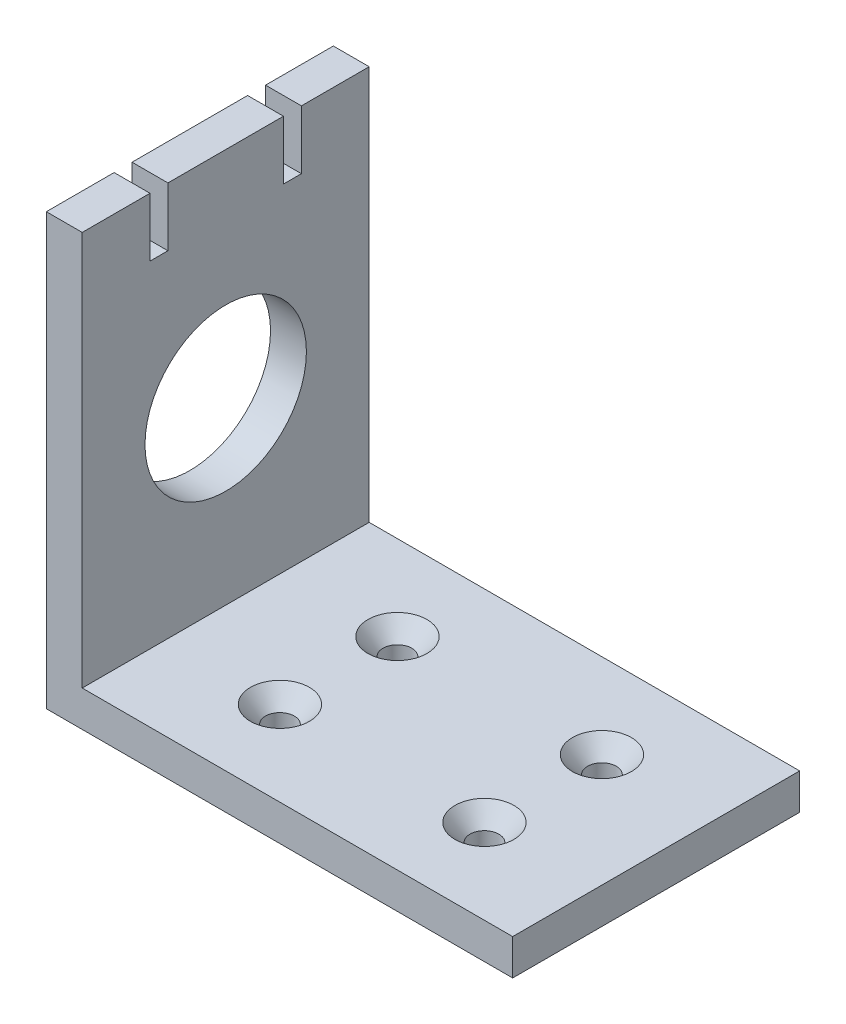
SolidWorks part; units mm, degrees
ref_plane "Front Plane" through (0, 0, 0) normal (0, 0, 1) x (1, 0, 0)
ref_plane "Top Plane" through (0, 0, 0) normal (0, 1, 0) x (1, 0, 0)
ref_plane "Right Plane" through (0, 0, 0) normal (1, 0, 0) x (0, 0, -1)
sketch "Sketch1" plane through (0, 0, 0) normal (1, 0, 0) x (0, 0, -1)
  line L1 (0, 0) -> (50.8, 0)
  line L2 (0, 0) -> (0, 76.2)
  line L3 (0, 76.2) -> (50.8, 76.2)
  line L4 (50.8, 0) -> (50.8, 76.2)
  dimension "D1" = 76.2
  dimension "D2" = 50.8
extrude "Boss-Extrude1" add sketch "Sketch1" along normal blind 6.35
sketch "Sketch2" plane through (6.35, 0, 0) normal (1, 0, 0) x (0, 0, -1)
  line L0 (50.8, 0) -> (50.8, 76.2) construction
  line L1 (0, 0) -> (50.8, 0)
  line L2 (0, 0) -> (0, 6.35)
  line L3 (0, 6.35) -> (50.8, 6.35)
  line L4 (50.8, 0) -> (50.8, 6.35)
  dimension "D1" = 6.35
extrude "Boss-Extrude2" add sketch "Sketch2" along normal blind 76.2
sketch "Sketch3" plane through (6.35, 0, 0) normal (1, 0, 0) x (0, 0, -1)
  line L0 (0, 0) -> (50.8, 0) construction
  line L1 (0, 76.2) -> (0, 6.35) construction
  circle A0 centre (25.4, 38.1) radius 14.2875
  dimension "D1" = 28.575
  dimension "D2" = 38.1
  dimension "D3" = 25.4
extrude "Cut-Extrude1" cut sketch "Sketch3" against normal through all
hole_wizard "CSK for #10 Flat Head Socket Cap Screw1" positions "Sketch10" profile "Sketch11" countersink size "#10" standard "ANSI Inch" end condition through all
sketch "Sketch10" plane through (0, 6.35, 0) normal (0, 1, 0) x (1, 0, 0)
  line L3 (82.55, 50.8) -> (6.35, 50.8) construction
  line L4 (82.55, 0) -> (6.35, 0) construction
  line L5 (6.35, 50.8) -> (6.35, 0) construction
  line L6 (6.35, 50.8) -> (6.35, 0) construction
  line L7 (82.55, 50.8) -> (82.55, 0) construction
  point P0 (26.35, 35.8)
  point P2 (62.55, 35.8)
  point P4 (62.55, 15)
  point P6 (26.35, 15)
  dimension "D1" = 15
  dimension "D2" = 15
  dimension "D3" = 15
  dimension "D4" = 15
  dimension "D5" = 20
  dimension "D6" = 20
  dimension "D7" = 20
  dimension "D8" = 20
sketch "Sketch11" plane through (26.35, 6.35, -35.8) normal (1, 0, 0) x (0, 0, 1)
  line L0 (0, 0) -> (0, 6.35)
  line L1 (0, 6.35) -> (2.5527, 6.35)
  line L2 (2.5527, 6.35) -> (2.5527, 3.068)
  line L3 (2.5527, 3.068) -> (5.2197, 0)
  line L5 (5.2197, 0) -> (0, 0)
  line L6 (-2.5527, 3.068) -> (-5.2197, 0) construction
  line L11 (0, -6.35) -> (0, 107.95) construction
  dimension "Thru Hole Dia." = 5.1054
  dimension "Thru Hole Depth" = 6.35
  dimension "Near C'Sink Dia." = 10.4394
  dimension "Near C'Sink Angle" = 82
sketch "Sketch12" plane through (6.35, 0, 0) normal (1, 0, 0) x (0, 0, -1)
  line L0 (50.8, 76.2) -> (0, 76.2) construction
  line L1 (35.625, 76.2) -> (38.8, 76.2)
  line L2 (35.625, 76.2) -> (35.625, 65.8)
  line L3 (35.625, 65.8) -> (38.8, 65.8)
  line L4 (38.8, 76.2) -> (38.8, 65.8)
  line L5 (50.8, 6.35) -> (50.8, 76.2) construction
  line L6 (25.4, 76.2) -> (25.4, 70.2338) construction
  line L7 (15.175, 65.8) -> (12, 65.8)
  line L8 (12, 76.2) -> (12, 65.8)
  line L9 (15.175, 76.2) -> (12, 76.2)
  line L10 (15.175, 76.2) -> (15.175, 65.8)
  dimension "D1" = 12
  dimension "D2" = 3.175
  dimension "D3" = 10.4
extrude "Cut-Extrude2" cut sketch "Sketch12" against normal through all
